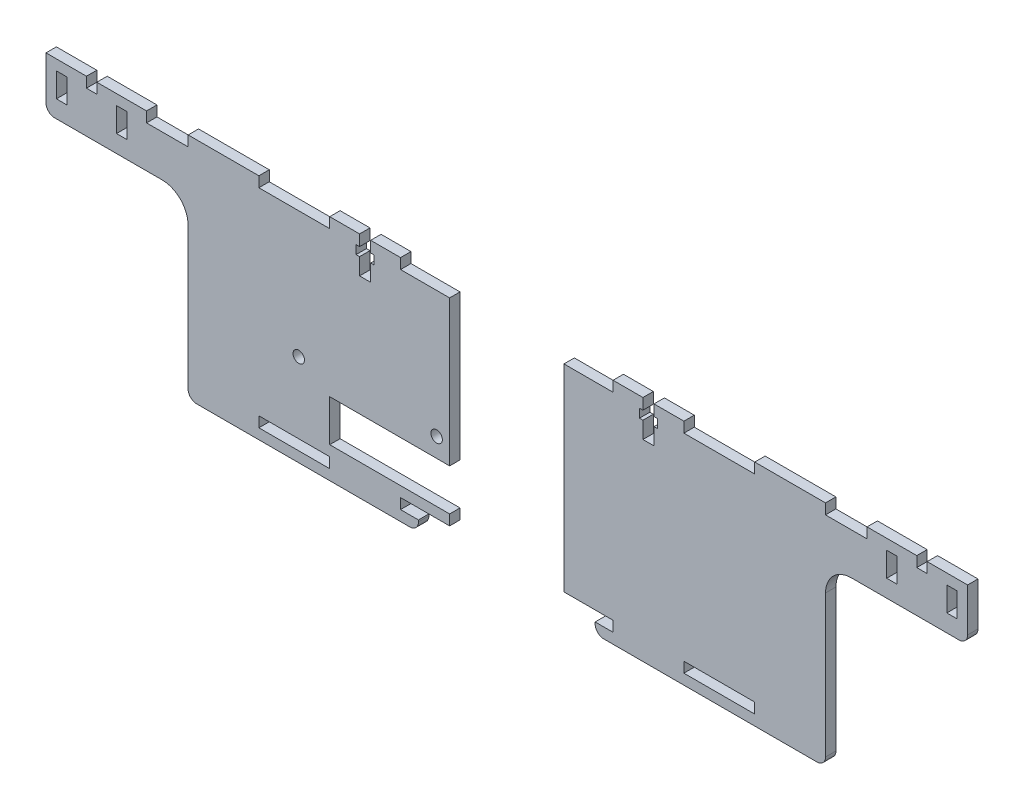
SolidWorks part; units mm, degrees
ref_plane "Front Plane" through (0, 0, 0) normal (0, 0, 1) x (1, 0, 0)
ref_plane "Top Plane" through (0, 0, 0) normal (0, 1, 0) x (1, 0, 0)
ref_plane "Right Plane" through (0, 0, 0) normal (1, 0, 0) x (0, 0, -1)
sketch "Sketch2" plane through (0, 0, 0) normal (0, 0, 1) x (1, 0, 0)
  line L0 (-133, 33) -> (133, 33)
  line L1 (133, 33) -> (133, 18)
  line L2 (133, 18) -> (92, 18)
  line L3 (92, 18) -> (92, -33)
  line L4 (92, -33) -> (-92, -33)
  line L5 (-92, -33) -> (-92, 18)
  line L6 (-92, 18) -> (-133, 18)
  line L7 (-133, 18) -> (-133, 33)
  point P2 (0, 33)
  dimension "D1" = 184
  dimension "D2" = 266
  dimension "D3" = 15
  dimension "D4" = 66
  dimension "D5" = 33
extrude "Boss-Extrude1" add sketch "Sketch2" along normal blind 3
sketch "Sketch3" plane through (0, 0, 3) normal (0, 0, 1) x (1, 0, 0)
  line L0 (130, 25.5) -> (133, 25.5) construction
  line L1 (-130, 23) -> (-127, 23)
  line L2 (-130, 23) -> (-130, 30)
  line L3 (-130, 30) -> (-127, 30)
  line L4 (-127, 23) -> (-127, 30)
  line L5 (-130, 23) -> (-127, 30) construction
  line L6 (-130, 30) -> (-127, 23) construction
  line L7 (127, 23) -> (130, 23)
  line L8 (127, 23) -> (127, 30)
  line L9 (127, 30) -> (130, 30)
  line L10 (130, 23) -> (130, 30)
  line L11 (127, 23) -> (130, 30) construction
  line L12 (127, 30) -> (130, 23) construction
  line L13 (133, 18) -> (133, 33) construction
  line L14 (-130, 26.5) -> (-133, 26.5) construction
  line L15 (-133, 33) -> (-133, 18) construction
  line L16 (-130, 30) -> (-130, 33) construction
  line L17 (133, 33) -> (-133, 33) construction
  line L18 (92, 18) -> (133, 18) construction
  line L19 (112.65, 26.5) -> (127, 26.5) construction
  line L20 (-92, -30) -> (-71.5556, -30) construction
  line L21 (-71.5556, -30) -> (-51.1111, -30)
  line L22 (-71.5556, -30) -> (-71.5556, -27)
  line L23 (-71.5556, -27) -> (-51.1111, -27)
  line L24 (-51.1111, -30) -> (-51.1111, -27)
  line L25 (-71.5556, -30) -> (-51.1111, -27) construction
  line L26 (-71.5556, -27) -> (-51.1111, -30) construction
  line L27 (-30.6667, -30) -> (-10.2222, -30)
  line L28 (-30.6667, -30) -> (-30.6667, -27)
  line L29 (-30.6667, -27) -> (-10.2222, -27)
  line L30 (-10.2222, -30) -> (-10.2222, -27)
  line L31 (-30.6667, -30) -> (-10.2222, -27) construction
  line L32 (-30.6667, -27) -> (-10.2222, -30) construction
  line L33 (10.2222, -30) -> (30.6667, -30)
  line L34 (10.2222, -30) -> (10.2222, -27)
  line L35 (10.2222, -27) -> (30.6667, -27)
  line L36 (30.6667, -30) -> (30.6667, -27)
  line L37 (10.2222, -30) -> (30.6667, -27) construction
  line L38 (10.2222, -27) -> (30.6667, -30) construction
  line L39 (51.1111, -30) -> (71.5556, -30)
  line L40 (51.1111, -30) -> (51.1111, -27)
  line L41 (51.1111, -27) -> (71.5556, -27)
  line L42 (71.5556, -30) -> (71.5556, -27)
  line L43 (51.1111, -30) -> (71.5556, -27) construction
  line L44 (51.1111, -27) -> (71.5556, -30) construction
  line L45 (-92, 18) -> (-92, -33) construction
  line L46 (-51.1111, -30) -> (-30.6667, -30) construction
  line L47 (-10.2222, -30) -> (10.2222, -30) construction
  line L48 (30.6667, -30) -> (51.1111, -30) construction
  line L49 (71.5556, -30) -> (92, -30) construction
  line L50 (92, -33) -> (92, 18) construction
  line L51 (-92, -33) -> (92, -33) construction
  line L52 (109.65, 23) -> (112.65, 23)
  line L57 (109.65, 23) -> (109.65, 30)
  line L58 (109.65, 30) -> (112.65, 30)
  line L63 (112.65, 23) -> (112.65, 30)
  line L64 (109.65, 23) -> (112.65, 30) construction
  line L69 (109.65, 30) -> (112.65, 23) construction
  line L70 (-112.65, 23) -> (-109.65, 23)
  line L75 (-112.65, 23) -> (-112.65, 30)
  line L76 (-112.65, 30) -> (-109.65, 30)
  line L81 (-109.65, 23) -> (-109.65, 30)
  line L82 (-112.65, 23) -> (-109.65, 30) construction
  line L87 (-112.65, 30) -> (-109.65, 23) construction
  line L88 (-127, 26.5) -> (-112.65, 26.5) construction
  line L89 (-51.1111, 30) -> (-30.6667, 30) construction
  line L90 (-71.5556, 30) -> (-51.1111, 30)
  line L91 (-71.5556, 30) -> (-71.5556, 33)
  line L92 (-71.5556, 33) -> (-51.1111, 33)
  line L93 (-51.1111, 30) -> (-51.1111, 33)
  line L94 (-71.5556, 30) -> (-51.1111, 33) construction
  line L99 (-71.5556, 33) -> (-51.1111, 30) construction
  line L100 (-30.6667, 30) -> (-10.2222, 30)
  line L105 (-30.6667, 30) -> (-30.6667, 33)
  line L106 (-30.6667, 33) -> (-10.2222, 33)
  line L107 (-10.2222, 30) -> (-10.2222, 33)
  line L108 (-30.6667, 30) -> (-10.2222, 33) construction
  line L109 (-30.6667, 33) -> (-10.2222, 30) construction
  line L110 (10.2222, 30) -> (30.6667, 30)
  line L111 (10.2222, 30) -> (10.2222, 33)
  line L112 (10.2222, 33) -> (30.6667, 33)
  line L113 (30.6667, 30) -> (30.6667, 33)
  line L114 (10.2222, 30) -> (30.6667, 33) construction
  line L115 (10.2222, 33) -> (30.6667, 30) construction
  line L116 (51.1111, 30) -> (71.5556, 30)
  line L117 (51.1111, 30) -> (51.1111, 33)
  line L118 (51.1111, 33) -> (71.5556, 33)
  line L119 (71.5556, 30) -> (71.5556, 33)
  line L120 (51.1111, 30) -> (71.5556, 33) construction
  line L121 (51.1111, 33) -> (71.5556, 30) construction
  line L122 (-10.2222, 30) -> (10.2222, 30) construction
  line L123 (30.6667, 30) -> (51.1111, 30) construction
  line L124 (71.5556, 30) -> (92, 30) construction
  line L125 (-71.5556, 30) -> (-92, 30) construction
  line L126 (92, 30) -> (112.4444, 30)
  line L127 (92, 30) -> (92, 33)
  line L128 (92, 33) -> (112.4444, 33)
  line L129 (112.4444, 30) -> (112.4444, 33)
  line L130 (92, 30) -> (112.4444, 33) construction
  line L131 (92, 33) -> (112.4444, 30) construction
  line L133 (-112.4444, 33) -> (-92, 33)
  line L134 (-112.4444, 33) -> (-112.4444, 30)
  line L135 (-112.4444, 30) -> (-92, 30)
  line L136 (-92, 33) -> (-92, 30)
  line L137 (-112.4444, 33) -> (-92, 30) construction
  line L138 (-112.4444, 30) -> (-92, 33) construction
  point P0 (-128.5, 26.5)
  point P5 (128.5, 26.5)
  point P18 (-111.15, 26.5)
  point P22 (111.15, 26.5)
  point P24 (-61.3333, -28.5)
  point P29 (-20.4444, -28.5)
  point P34 (20.4444, -28.5)
  point P39 (61.3333, -28.5)
  point P63 (-61.3333, 31.5)
  point P68 (-20.4444, 31.5)
  point P73 (20.4444, 31.5)
  point P78 (61.3333, 31.5)
  point P83 (102.2222, 31.5)
  point P89 (-102.2222, 31.5)
  line M16 (133, 33) -> (-133, 33)
  dimension "D1" = 3
  dimension "D2" = 3
  dimension "D3" = 3
  dimension "D4" = 14.35
  dimension "D5" = 5
extrude "Cut-Extrude1" cut sketch "Sketch3" against normal through all both and the other way through all contours L1 L4 L3 L2 | L70 L81 L76 L75 | L90 L93 L91 M16 | L100 L107 L105 M16 | L110 L113 L111 M16 | L116 L119 L117 M16 | L7 L10 L9 L8 | L52 L63 L58 L57 | L21 L24 L23 L22 | L27 L30 L29 L28 | L33 L36 L35 L34 | L39 L42 L41 L40
fillet "Fillet1" radius 7.5 2 edges at (-92, 18, 1.5) (92, 18, 1.5)
sketch "Sketch4" plane through (0, 0, 3) normal (0, 0, 1) x (1, 0, 0)
  line L1 (-42.4889, 22.5) -> (-39.2889, 22.5)
  line L2 (-42.4889, 22.5) -> (-42.4889, 33)
  line L3 (-42.4889, 33) -> (-39.2889, 33)
  line L4 (-39.2889, 22.5) -> (-39.2889, 33)
  line L5 (-42.4889, 22.5) -> (-39.2889, 33) construction
  line L6 (-42.4889, 33) -> (-39.2889, 22.5) construction
  line L8 (39.2889, 22.5) -> (42.4889, 22.5)
  line L9 (39.2889, 22.5) -> (39.2889, 33)
  line L10 (39.2889, 33) -> (42.4889, 33)
  line L11 (42.4889, 22.5) -> (42.4889, 33)
  line L12 (39.2889, 22.5) -> (42.4889, 33) construction
  line L13 (39.2889, 33) -> (42.4889, 22.5) construction
  line L14 (40.8889, 33) -> (40.8889, 29.825) construction
  line L15 (38.2889, 29.825) -> (43.4889, 29.825)
  line L16 (38.2889, 29.825) -> (38.2889, 27.325)
  line L17 (38.2889, 27.325) -> (43.4889, 27.325)
  line L18 (43.4889, 29.825) -> (43.4889, 27.325)
  line L19 (38.2889, 29.825) -> (43.4889, 27.325) construction
  line L20 (38.2889, 27.325) -> (43.4889, 29.825) construction
  line L21 (-43.4889, 29.825) -> (-38.2889, 29.825)
  line L22 (-43.4889, 29.825) -> (-43.4889, 27.325)
  line L23 (-43.4889, 27.325) -> (-38.2889, 27.325)
  line L24 (-38.2889, 29.825) -> (-38.2889, 27.325)
  line L25 (-43.4889, 29.825) -> (-38.2889, 27.325) construction
  line L26 (-43.4889, 27.325) -> (-38.2889, 29.825) construction
  line L27 (-40.8889, 33) -> (-40.8889, 29.825) construction
  line L28 (51.1111, 33) -> (30.6667, 33) construction
  line L29 (-30.6667, 33) -> (-51.1111, 33) construction
  point P0 (-40.8889, 27.75)
  point P7 (40.8889, 27.75)
  point P14 (40.8889, 28.575)
  point P19 (-40.8889, 28.575)
  point P40 (-40.8889, 33)
  point P41 (40.8889, 33)
  dimension "D1" = 2.5
  dimension "D2" = 5.2
  dimension "D3" = 3.2
  dimension "D4" = 10.5
  dimension "D5" = 3.175
extrude "Cut-Extrude2" cut sketch "Sketch4" against normal through all both and the other way through all contours L8 L11 L10 L9 | L16 L17 L18 L15 | L1 L4 L3 L2 | L24 L23 L22 L21
sketch "Sketch5" plane through (0, 0, 3) normal (0, 0, 1) x (1, 0, 0)
  line L1 (-16.5, -33) -> (16.5, -33)
  line L2 (-16.5, -33) -> (-16.5, 33)
  line L3 (-16.5, 33) -> (16.5, 33)
  line L4 (16.5, -33) -> (16.5, 33)
  line L5 (-16.5, -33) -> (16.5, 33) construction
  line L6 (-16.5, 33) -> (16.5, -33) construction
  line L7 (-92, -33) -> (92, -33) construction
  line L8 (10.2222, 33) -> (-10.2222, 33) construction
  point P0 (0, 0)
  dimension "D1" = 33
extrude "Cut-Extrude3" cut sketch "Sketch5" against normal through all both and the other way through all
sketch "Sketch6" plane through (0, 0, 3) normal (0, 0, 1) x (1, 0, 0)
  line L2 (-51.1111, -24) -> (-51.1111, -12)
  line L4 (-16.5, -24) -> (-16.5, -12)
  line L5 (-16.5, -27) -> (-16.5, 30) construction
  line L7 (-51.1111, -24) -> (-51.1111, -27) construction
  line L9 (30.6667, -27) -> (30.6667, -30) construction
  line L11 (-16.5, -27) -> (-16.5, 30) construction
  line L12 (-51.1111, -12) -> (-16.5, -12)
  line L13 (-51.1111, -24) -> (-16.5, -24)
  line L14 (-16.5, -27) -> (-30.6667, -27) construction
  line L15 (-51.1111, -27) -> (-51.1111, -30) construction
  circle A0 centre (-20.25, -6.5) radius 1.65
  circle A1 centre (-60.05, -6.5) radius 1.65
  point P19 (-16.5, -18)
  point P20 (-51.1111, -18)
  dimension "D5" = 3.3
  dimension "D1" = 12
  dimension "D2" = 5.5
  dimension "D3" = 3.75
  dimension "D4" = 39.8
  dimension "D6" = 0
extrude "Cut-Extrude4" cut sketch "Sketch6" against normal through all both and the other way through all
sketch "Sketch9" plane through (0, 0, 3) normal (0, 0, 1) x (1, 0, 0)
  line L0 (16.5, -33) -> (92, -33) construction
  line L1 (-25.5, -30) -> (-16.5, -30)
  line L2 (-25.5, -30) -> (-25.5, -33)
  line L3 (-25.5, -33) -> (-16.5, -33)
  line L4 (-16.5, -30) -> (-16.5, -33)
  line L5 (-25.5, -30) -> (-16.5, -33) construction
  line L6 (-25.5, -33) -> (-16.5, -30) construction
  line L7 (25.5, -30) -> (16.5, -30)
  line L8 (25.5, -30) -> (25.5, -33)
  line L9 (25.5, -33) -> (16.5, -33)
  line L10 (16.5, -30) -> (16.5, -33)
  line L11 (25.5, -30) -> (16.5, -33) construction
  line L12 (25.5, -33) -> (16.5, -30) construction
  line L13 (30.6667, -30) -> (16.5, -30) construction
  line L14 (16.5, -30) -> (16.5, -33) construction
  point P0 (-21, -31.5)
  point P6 (21, -31.5)
  dimension "D1" = 9
extrude "Cut-Extrude7" cut sketch "Sketch9" against normal through all both and the other way through all
fillet "Fillet2" radius 2.5 3 edges at (92, -33, 1.5) (133, 18, 1.5) (25.5, -33, 1.5)
fillet "Fillet3" radius 2.5 3 edges at (-133, 18, 1.5) (-92, -33, 1.5) (-25.5, -33, 1.5)
sketch "Sketch7" plane through (0, 0, 0) normal (0, 0, 1) x (1, 0, 0)
  line L0 (-71.5556, 33) -> (-133, 33) construction
  line L1 (-121.325, 30) -> (-118.325, 30)
  line L2 (-121.325, 30) -> (-121.325, 33)
  line L3 (-121.325, 33) -> (-118.325, 33)
  line L4 (-118.325, 30) -> (-118.325, 33)
  line L5 (-121.325, 30) -> (-118.325, 33) construction
  line L6 (-121.325, 33) -> (-118.325, 30) construction
  line L7 (133, 33) -> (71.5556, 33) construction
  line L8 (118.325, 30) -> (121.325, 30)
  line L9 (118.325, 30) -> (118.325, 33)
  line L10 (118.325, 33) -> (121.325, 33)
  line L11 (121.325, 30) -> (121.325, 33)
  line L12 (118.325, 30) -> (121.325, 33) construction
  line L13 (118.325, 33) -> (121.325, 30) construction
  line L14 (-109.65, 30) -> (-112.65, 30) construction
  line L15 (112.65, 26.5) -> (127, 26.5) construction
  line L16 (112.65, 30) -> (112.65, 23) construction
  line L17 (127, 30) -> (127, 23) construction
  line L18 (-127, 26.5) -> (-112.65, 26.5) construction
  line L19 (-127, 30) -> (-127, 23) construction
  line L20 (-112.65, 30) -> (-112.65, 23) construction
  line L21 (-71.5556, 33) -> (-133, 33) construction
  line L22 (-103.975, 30) -> (-93.975, 30)
  line L23 (-103.975, 30) -> (-103.975, 33)
  line L24 (-103.975, 33) -> (-93.975, 33)
  line L25 (-93.975, 30) -> (-93.975, 33)
  line L26 (-103.975, 30) -> (-93.975, 33) construction
  line L27 (-103.975, 33) -> (-93.975, 30) construction
  line L28 (133, 33) -> (71.5556, 33) construction
  line L29 (103.975, 30) -> (93.975, 30)
  line L30 (103.975, 30) -> (103.975, 33)
  line L31 (103.975, 33) -> (93.975, 33)
  line L32 (93.975, 30) -> (93.975, 33)
  line L33 (103.975, 30) -> (93.975, 33) construction
  line L34 (103.975, 33) -> (93.975, 30) construction
  line L35 (-98.975, 31.5) -> (98.975, 31.5) construction
  line L36 (118.325, 30) -> (103.975, 30) construction
  line L37 (112.65, 23) -> (109.65, 23) construction
  point P0 (-119.825, 31.5)
  point P7 (119.825, 31.5)
  point P28 (-119.825, 26.5)
  point P29 (119.825, 26.5)
  point P30 (-98.975, 31.5)
  point P37 (98.975, 31.5)
  point P46 (0, 31.5)
  point P53 (111.15, 23)
  point P54 (111.15, 30)
  dimension "D1" = 10
extrude "Cut-Extrude5" cut sketch "Sketch7" against normal through all both and the other way through all
sketch "Sketch8" plane through (0, 0, 3) normal (0, 0, 1) x (1, 0, 0)
  line L0 (93.975, 30) -> (103.975, 30) construction
  line L1 (-91.975, 30) -> (-93.975, 30)
  line L2 (-91.975, 30) -> (-91.975, 33)
  line L3 (-91.975, 33) -> (-93.975, 33)
  line L4 (-93.975, 30) -> (-93.975, 33)
  line L5 (-91.975, 30) -> (-93.975, 33) construction
  line L6 (-91.975, 33) -> (-93.975, 30) construction
  line L7 (91.975, 30) -> (93.975, 30)
  line L8 (91.975, 30) -> (91.975, 33)
  line L9 (91.975, 33) -> (93.975, 33)
  line L10 (93.975, 30) -> (93.975, 33)
  line L11 (91.975, 30) -> (93.975, 33) construction
  line L12 (91.975, 33) -> (93.975, 30) construction
  point P0 (-92.975, 31.5)
  point P6 (92.975, 31.5)
  dimension "D1" = 2
extrude "Cut-Extrude6" cut sketch "Sketch8" against normal through all both and the other way through all
